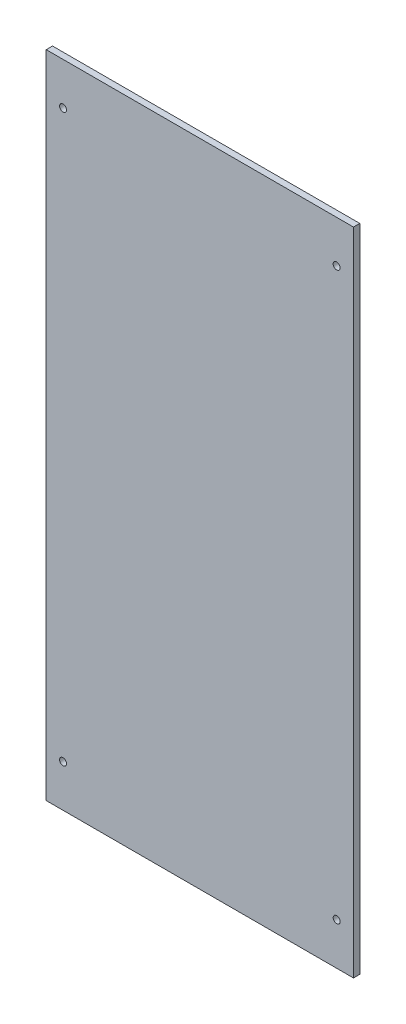
SolidWorks part; units mm, degrees
ref_plane "Plan de face" through (0, 0, 0) normal (0, 0, 1) x (1, 0, 0)
ref_plane "Plan de dessus" through (0, 0, 0) normal (0, 1, 0) x (1, 0, 0)
ref_plane "Plan de droite" through (0, 0, 0) normal (1, 0, 0) x (0, 0, -1)
sketch "Esquisse1" plane through (0, 0, 0) normal (0, 0, 1) x (1, 0, 0)
  line L1 (0, 0) -> (146, 0)
  line L2 (0, 0) -> (0, 309)
  line L3 (0, 309) -> (146, 309)
  line L4 (146, 0) -> (146, 309)
  dimension "D1" = 309
  dimension "D2" = 146
extrude "Boss.-Extru.1" add sketch "Esquisse1" along normal blind 3
sketch "Esquisse2" plane through (0, 0, 3) normal (0, 0, 1) x (1, 0, 0)
  line L0 (0, 309) -> (0, 0) construction
  line L1 (146, 309) -> (0, 309) construction
  line L4 (0, 154.5) -> (146, 154.5) construction
  line L5 (146, 0) -> (146, 309) construction
  line L6 (73, 154.5) -> (73, 214.2408) construction
  circle A0 centre (8, 289) radius 1.65
  circle A1 centre (138, 289) radius 1.65
  circle A2 centre (138, 20) radius 1.65
  circle A3 centre (8, 20) radius 1.65
  dimension "D2" = 3.3
  dimension "D1" = 65
  dimension "D3" = 20
extrude "Enlèv. mat.-Extru.1" cut sketch "Esquisse2" against normal through all
